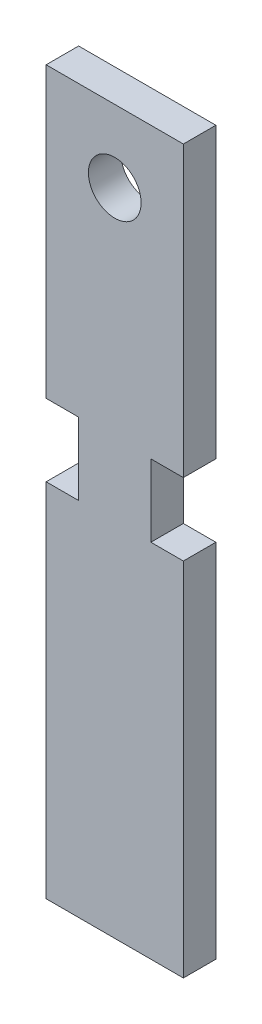
SolidWorks part; units mm, degrees
ref_plane "Front Plane" through (0, 0, 0) normal (0, 0, 1) x (1, 0, 0)
ref_plane "Top Plane" through (0, 0, 0) normal (0, 1, 0) x (1, 0, 0)
ref_plane "Right Plane" through (0, 0, 0) normal (1, 0, 0) x (0, 0, -1)
sketch "Sketch1" plane through (0, 0, 0) normal (0, 0, 1) x (1, 0, 0)
  line L0 (-25.4, 63.5) -> (-25.4, -63.5)
  line L5 (-25.4, 63.5) -> (25.4, 63.5)
  line L6 (-25.4, -63.5) -> (25.4, -63.5)
  line L7 (25.4, 63.5) -> (25.4, -63.5)
  line L8 (-25.4, 0) -> (25.4, 0) construction
  point P0 (0, 0)
  point P13 (-25.4, 0)
  point P14 (0, 0)
  dimension "D3" = 50.8
extrude "Boss-Extrude1" add sketch "Sketch1" along normal blind 5.715
sketch "Sketch2" plane through (0, 0, 5.715) normal (0, 0, 1) x (1, 0, 0)
  line L4 (-12.065, 0) -> (-6.35, 0)
  line L5 (-12.065, 0) -> (-12.065, 12.7)
  line L6 (-12.065, 12.7) -> (-6.35, 12.7)
  line L7 (-6.35, 0) -> (-6.35, 12.7)
  line L8 (-12.065, 0) -> (-6.35, 12.7) construction
  line L9 (-12.065, 12.7) -> (-6.35, 0) construction
  line L11 (0, -3.1432) -> (0, 3.1432) construction
  line L12 (12.065, 0) -> (6.35, 0)
  line L13 (12.065, 0) -> (12.065, 12.7)
  line L14 (12.065, 12.7) -> (6.35, 12.7)
  line L15 (6.35, 0) -> (6.35, 12.7)
  line L17 (-25.4, -63.5) -> (25.4, -63.5) construction
  circle A0 centre (0, 50.8) radius 4.6355
  point P3 (0, -63.5)
  point P5 (-9.2075, 6.35)
  dimension "D2" = 9.271
  dimension "D1" = 114.3
  dimension "D3" = 63.5
  dimension "D4" = 12.7
  dimension "D5" = 5.715
  dimension "D6" = 6.35
  dimension "D7" = 6.35
extrude "Cut-Extrude1" cut sketch "Sketch2" against normal through all
sketch "Sketch3" plane through (0, 0, 5.715) normal (0, 0, 1) x (1, 0, 0)
  line L0 (-12.065, 63.5) -> (12.065, 63.5)
  line L1 (25.4, 63.5) -> (-25.4, 63.5) construction
  line L2 (-12.065, 63.5) -> (-12.065, -63.5)
  line L3 (-25.4, -63.5) -> (25.4, -63.5) construction
  line L4 (12.065, 63.5) -> (12.065, -63.5)
  line L5 (-12.065, -63.5) -> (12.065, -63.5)
  line L6 (-12.065, 12.7) -> (-12.065, 0) construction
  line L7 (12.065, 0) -> (12.065, 12.7) construction
  line M9 (-12.065, 0) -> (-12.065, 12.7)
  line M11 (12.065, 12.7) -> (12.065, 0)
  line M14 (25.4, 63.5) -> (-25.4, 63.5)
  line M15 (-25.4, 63.5) -> (-25.4, -63.5)
  line M16 (-25.4, -63.5) -> (25.4, -63.5)
  line M17 (25.4, -63.5) -> (25.4, 63.5)
extrude "Cut-Extrude2" cut sketch "Sketch3" against normal through all contours L2 M14 M15 M16 M9 | L4 M14 M11 M16 M17
